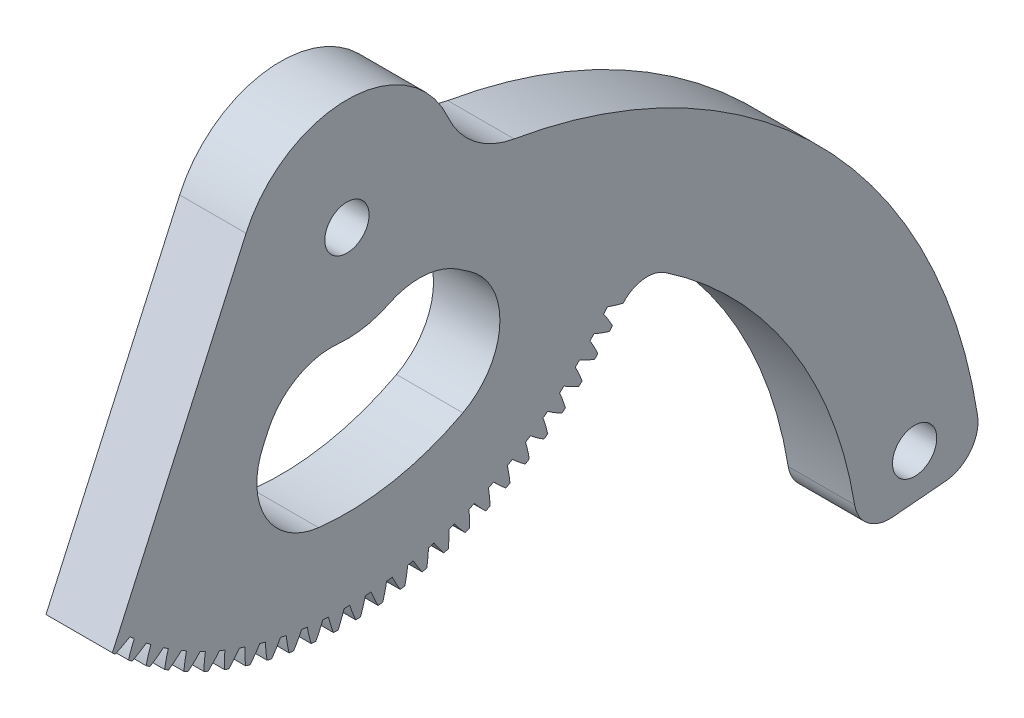
SolidWorks part; units mm, degrees
ref_plane "Plane1" through (0, 0, 0) normal (0, 0, 1) x (1, 0, 0)
ref_plane "Plane2" through (0, 0, 0) normal (0, 1, 0) x (1, 0, 0)
ref_plane "Plane3" through (0, 0, 0) normal (1, 0, 0) x (0, 0, -1)
sketch "HoldingSke" plane through (0, 0, 0) normal (0, 1, 0) x (1, 0, 0)
  line L0 (0, 0) -> (-0.1045, -0.9945)
  line L1 (-15, 0) -> (100, 0) construction
  line L2 (0, 0) -> (-2.1039, 2.3779)
  line L3 (0, 0) -> (-11.863, 4.5341)
  line L4 (0, 0) -> (-0.9027, 8.5887)
  line L5 (0, 0) -> (-46.8476, -17.4728)
  line L6 (0, 0) -> (-10.5278, -7.1032)
  line L7 (-2.1039, 2.3779) -> (8.6586, 51.2059)
  line L8 (-76.2, 54.61) -> (-76.1, 54.61)
  line L9 (-71.009, 38.7566) -> (-53.1078, 45.2721)
  line L10 (-76.2, 71.12) -> (104.1128, 71.12)
  line L11 (0, 0) -> (-12.7, 0)
  line L12 (-76.2, 101.6) -> (-76.162, 101.6)
  line L13 (24.9733, 27.94) -> (52.9518, 28.4284)
  line L14 (24.9733, 27.94) -> (24.9743, 27.94)
  line L15 (24.9733, 27.94) -> (100.4006, 29.5858)
  line L16 (-63.627, -1) -> (-12.827, -1)
  circle A0 centre (0, 0) radius 0.4
  circle A1 centre (0, 0) radius 37.5
  circle A2 centre (0, 0) radius 37.5
  circle A3 centre (0, 0) radius 0.4
  dimension "MHD" = 75
  dimension "Hub_dia" = 75
  dimension "Bore" = 0.8
  dimension "MBD" = 0.8
  dimension "Num_teeth" = 96
  dimension "Pitch" = 1
  dimension "Overall_len" = 50
  dimension "Show_teeth" = 96
  dimension "Thickness" = 12.7
  dimension "OAL" = 50.0001
  dimension "T_dim" = 0.1
  dimension "Ap" = 20
  dimension "H" = 19.05
  dimension "Pitch_radius" = 180.3128
  dimension "Width" = 12.7
  dimension "Backlash" = 0.038
  dimension "Addendum_fac" = 1
  dimension "Dedendum_fac" = 1.25
  dimension "Clearance_fac" = 0.25
  dimension "Dedendum_add" = 0.001
  dimension "Module" = 1
sketch "BasProSke" plane through (0, 0, 0) normal (0, 1, 0) x (1, 0, 0)
  line L0 (-10, 0) -> (60, 0) construction
  line L1 (0, 0) -> (0, 49)
  line L2 (0, 0) -> (12.7, 0)
  line L3 (12.7, 0) -> (12.7, 49)
  line L4 (12.7, 49) -> (0, 49)
  dimension "Thickness" = 12.7
  dimension "Diameter" = 98
revolve "Base-Revolve" add sketch "BasProSke" angle 360 about L0
sketch "TooCutSke" plane through (0, 0, 0) normal (1, 0, 0) x (0, 0, -1)
  line L1 (0, 0) -> (0, 107) construction
  line L2 (0, 0) -> (-0.8519, 47.9924) construction
  line L3 (0, 0) -> (-3.1407, 95.9378) construction
  line L4 (-0.8519, 47.9924) -> (-1.5703, 47.9689) construction
  arc A0 (0.4157, 46.7472) -> (-0.4157, 46.7472) centre (0, 0) ccw
  arc A1 (1.2815, 49.0086) -> (-1.2815, 49.0086) centre (0, 0) ccw
  circle A2 centre (0, 0) radius 48 construction
  circle A3 centre (0, 0) radius 45.1052 construction
  arc A4 (-0.4157, 46.7472) -> (-1.2815, 49.0086) centre (-18.7436, 41.0264) ccw
  arc A5 (1.2815, 49.0086) -> (0.4157, 46.7472) centre (18.7436, 41.0264) ccw
  dimension "Root_dia" = 93.498
  dimension "Overcut_dia" = 98.0508
  dimension "Pitch_dia" = 96
  dimension "Base_dia" = 90.2105
  dimension "Flank_rad" = 19.2
  dimension "Half_ang" = 1.875
  dimension "Half_CT" = 0.7189
extrude "ToothCut" cut sketch "TooCutSke" along normal through all
fillet "Breaks" [suppressed] radius 0.02
fillet "RootFillets" [suppressed] radius 0.251
pattern_circular "TeethCuts" count 96 every 3.75 about axis through (-10, 0, 0) along (1, 0, 0) of "ToothCut", "RootFillets", "Breaks"
sketch "HubNeaOneSke" plane through (0, 0, 0) normal (-1, 0, 0) x (0, 0, 1)
  circle A0 centre (0, 0) radius 37.5
  dimension "Diameter" = 75
extrude "HubNearOne" [suppressed] add sketch "HubNeaOneSke" along normal blind 37.3001
sketch "HubNeaBotSke" plane through (0, 0, 0) normal (-1, 0, 0) x (0, 0, 1)
  circle A0 centre (0, 0) radius 37.5
  dimension "Diameter" = 75
extrude "HubNearBoth" [suppressed] add sketch "HubNeaBotSke" along normal blind 18.65
ref_plane "FarPln" through (12.7, 0, 0) normal (1, 0, 0) x (0, 0, -1)
sketch "HubFarSke" plane through (12.7, 0, 0) normal (1, 0, 0) x (0, 0, -1)
  circle A0 centre (0, 0) radius 37.5
  dimension "Diameter" = 75
extrude "HubFar" [suppressed] add sketch "HubFarSke" along normal blind 18.65
sketch "BorSke" plane through (0, 0, 0) normal (1, 0, 0) x (0, 0, -1)
  circle A0 centre (0, 0) radius 0.4
  dimension "Diameter" = 0.8
extrude "Bore" cut sketch "BorSke" along normal mid plane 100.0001
sketch "KeySke" plane through (0, 0, 0) normal (1, 0, 0) x (0, 0, -1)
  line L0 (-0.05, 0) -> (-0.05, 0.5)
  line L1 (-0.05, 0.5) -> (0.05, 0.5)
  line L2 (0.05, 0.5) -> (0.05, 0)
  line L3 (0, 0) -> (0, 34) construction
  line L4 (-0.05, 0) -> (0.05, 0)
  dimension "Offset" = 0.5
  dimension "Width" = 0.1
extrude "Keyway" [suppressed] cut sketch "KeySke" along normal mid plane 100.0001
pattern_circular "Keyway2" [suppressed] count 2 every 90 about axis through (-10, 0, 0) along (1, 0, 0)
sketch "Croquis2" plane through (12.7, 0, 0) normal (1, 0, 0) x (0, 0, -1)
  line L4 (78.2913, -74.7181) -> (85.9012, -74.0523)
  line L5 (-14.4729, 6.923) -> (-33.6475, -35.6208)
  arc A0 (-33.6475, -35.6208) -> (40.4538, -27.7628) centre (0, 0.4) ccw
  arc A1 (48.3959, -8.954) -> (40.4538, -27.7628) centre (0, 0.4) ccw
  arc A2 (-33.7385, -35.5347) -> (-33.252, -35.9904) centre (0, 0) ccw construction
  arc A66 (85.9012, -74.0523) -> (90.4783, -68.2125) centre (85.4584, -68.9917) ccw
  arc A67 (90.4783, -68.2125) -> (23.9847, -0.5832) centre (10.16, -80.6788) ccw
  arc A68 (14.5249, 6.8066) -> (23.9847, -0.5832) centre (26.1448, 11.9318) ccw
  arc A69 (14.5249, 6.8066) -> (-14.4729, 6.923) centre (0, 0.4) ccw
  arc A96 (45.6754, -28.0395) -> (40.4538, -27.7628) centre (42.8342, -32.2506) ccw
  arc A97 (72.8346, -70.4738) -> (45.6754, -28.0395) centre (10.16, -80.6788) ccw
  arc A98 (72.8346, -70.4738) -> (78.2913, -74.7181) centre (77.8486, -69.6574) ccw
extrude "Cortar-Extruir1" cut sketch "Croquis2" against normal through all contours A69 A68 A67 A1 L5
sketch "Croquis3" plane through (12.7, 0, 0) normal (1, 0, 0) x (0, 0, -1)
  line L0 (78.2913, -74.7181) -> (85.9012, -74.0523) construction
  line L1 (78.2913, -74.7181) -> (85.9012, -74.0523)
  line L2 (23.9847, -0.5832) -> (26.1016, -24.7798)
  line L4 (39.6344, -28.8117) -> (26.1016, -24.7798)
  arc A1 (90.4783, -68.2125) -> (23.9847, -0.5832) centre (10.16, -80.6788) ccw construction
  arc A2 (85.9012, -74.0523) -> (90.4783, -68.2125) centre (85.4584, -68.9917) ccw construction
  arc A3 (72.8346, -70.4738) -> (78.2913, -74.7181) centre (77.8486, -69.6574) ccw construction
  arc A4 (72.8346, -70.4738) -> (45.6754, -28.0395) centre (10.16, -80.6788) ccw construction
  arc A6 (90.4783, -68.2125) -> (23.9847, -0.5832) centre (10.16, -80.6788) ccw
  arc A7 (85.9012, -74.0523) -> (90.4783, -68.2125) centre (85.4584, -68.9917) ccw
  arc A8 (72.8346, -70.4738) -> (78.2913, -74.7181) centre (77.8486, -69.6574) ccw
  arc A9 (72.8346, -70.4738) -> (45.6754, -28.0395) centre (10.16, -80.6788) ccw
  arc A13 (39.6344, -28.8117) -> (45.6754, -28.0395) centre (43.0946, -31.8647) cw
extrude "Saliente-Extruir1" add sketch "Croquis3" against normal through all
sketch "Croquis4" plane through (12.7, 0, 0) normal (1, 0, 0) x (0, 0, -1)
  line L0 (78.2913, -74.7181) -> (85.9012, -74.0523) construction
  circle A0 centre (0, 0.4) radius 3.175
  circle A1 centre (81.4431, -68.0681) radius 3.175
  arc A2 (90.4783, -68.2125) -> (23.9847, -0.5832) centre (10.16, -80.6788) ccw construction
  arc A3 (90.4783, -68.2125) -> (23.9847, -0.5832) centre (10.16, -80.6788) ccw construction
  circle A4 centre (10.16, -80.6788) radius 72.39 construction
  circle A5 centre (10.16, -80.6788) radius 81.715 construction
  arc A6 (14.5249, 6.8066) -> (-14.4729, 6.923) centre (0, 0.4) ccw construction
  dimension "D1" = 6.35
  dimension "D2" = 6.35
  dimension "D3" = 144.78
  dimension "D4" = 163.43
extrude "Cortar-Extruir2" cut sketch "Croquis4" against normal through all
sketch "Croquis5" plane through (0, 0, 0) normal (1, 0, 0) x (0, 0, -1)
  circle A1 centre (81.4431, -68.0681) radius 5
  dimension "D1" = 10
extrude "Cortar-Extruir3" cut sketch "Croquis5" along normal blind 6
ref_plane "Plano1" through (6.35, 0, 0) normal (1, 0, 0) x (0, 0, -1)
sketch "Croquis6" plane through (6.35, 0, 0) normal (1, 0, 0) x (0, 0, -1)
  circle A0 centre (0, 0.4) radius 49.2915 construction
  circle A1 centre (0, 0.4) radius 48.2915
  dimension "D1" = 1
sketch "Croquis7" plane through (12.7, 0, 0) normal (1, 0, 0) x (0, 0, -1)
  line L0 (-12.0435, -20.8056) -> (-11.3475, -19.2613)
  line L1 (17.5581, -13.8325) -> (16.0371, -12.8013)
  arc A0 (-1.2964, -13.414) -> (6.0586, -12.082) centre (0, 0.4) ccw
  arc A1 (-4.0752, -34.8484) -> (16.6343, -30.9426) centre (0, 0.4) ccw
  arc A2 (17.5581, -13.8325) -> (16.6343, -30.9426) centre (11.9463, -22.1095) cw
  arc A3 (-12.0435, -20.8056) -> (-4.0752, -34.8484) centre (-2.9267, -24.9145) ccw
  arc A4 (-11.3475, -19.2613) -> (-1.2964, -13.414) centre (-2.2307, -23.3703) cw
  arc A5 (16.0371, -12.8013) -> (6.0586, -12.082) centre (10.4253, -21.0782) ccw
  dimension "D1" = 10
extrude "Cortar-Extruir4" cut sketch "Croquis7" against normal up to surface (12.7 mm away)
sketch "Croquis11" plane through (12.7, 0, 0) normal (1, 0, 0) x (0, 0, -1)
  line L2 (78.2913, -74.7181) -> (85.9012, -74.0523)
  line L3 (-14.4729, 6.923) -> (-33.6475, -35.6208)
  line L4 (78.2913, -74.7181) -> (85.9012, -74.0523)
  line L5 (-14.4729, 6.923) -> (-33.6475, -35.6208)
  arc A111 (36.834, -28.7876) -> (37.3401, -28.1281) centre (0, 0) ccw
  arc A112 (37.3401, -28.1281) -> (39.6344, -28.8117) centre (43.9588, -10.105) ccw
  arc A113 (45.6754, -28.0395) -> (39.6344, -28.8117) centre (43.0946, -31.8647) ccw
  arc A114 (72.8346, -70.4738) -> (45.6754, -28.0395) centre (10.16, -80.6788) ccw
  arc A115 (72.8346, -70.4738) -> (78.2913, -74.7181) centre (77.8486, -69.6574) ccw
  arc A116 (85.9012, -74.0523) -> (90.4783, -68.2125) centre (85.4584, -68.9917) ccw
  arc A117 (90.4783, -68.2125) -> (23.9847, -0.5832) centre (10.16, -80.6788) ccw
  arc A118 (14.5249, 6.8066) -> (23.9847, -0.5832) centre (26.1448, 11.9318) ccw
  arc A119 (14.5249, 6.8066) -> (-14.4729, 6.923) centre (0, 0.4) ccw
  arc A120 (-33.6475, -35.6208) -> (-33.252, -35.9904) centre (0, 0) ccw
  arc A121 (-33.252, -35.9904) -> (-31.1351, -34.8723) centre (-41.1427, -18.4867) ccw
  arc A122 (-31.1351, -34.8723) -> (-30.51, -35.4204) centre (0, 0) ccw
  arc A123 (-30.51, -35.4204) -> (-31.3422, -37.6652) centre (-12.9584, -43.2037) ccw
  arc A124 (-31.3422, -37.6652) -> (-30.8269, -38.0881) centre (0, 0) ccw
  arc A125 (-30.8269, -38.0881) -> (-28.7876, -36.834) centre (-39.8455, -21.138) ccw
  arc A126 (-28.7876, -36.834) -> (-28.1281, -37.3401) centre (0, 0) ccw
  arc A127 (-28.1281, -37.3401) -> (-28.8117, -39.6344) centre (-10.105, -43.9588) ccw
  arc A128 (-28.8117, -39.6344) -> (-28.2698, -40.0227) centre (0, 0) ccw
  arc A129 (-28.2698, -40.0227) -> (-26.3169, -38.6379) centre (-38.3777, -23.6988) ccw
  arc A130 (-26.3169, -38.6379) -> (-25.6257, -39.0998) centre (0, 0) ccw
  arc A131 (-25.6257, -39.0998) -> (-26.1578, -41.4339) centre (-7.2083, -44.5255) ccw
  arc A132 (-26.1578, -41.4339) -> (-25.5917, -41.7859) centre (0, 0) ccw
  arc A133 (-25.5917, -41.7859) -> (-23.7336, -40.2764) centre (-36.7456, -26.1581) ccw
  arc A134 (-23.7336, -40.2764) -> (-23.0136, -40.6921) centre (0, 0) ccw
  arc A135 (-23.0136, -40.6921) -> (-23.3918, -43.056) centre (-4.2808, -44.9017) ccw
  arc A136 (-23.3918, -43.056) -> (-22.804, -43.3703) centre (0, 0) ccw
  arc A137 (-22.804, -43.3703) -> (-21.0485, -41.7424) centre (-34.9561, -28.5053) ccw
  arc A138 (-21.0485, -41.7424) -> (-20.3029, -42.1101) centre (0, 0) ccw
  arc A139 (-20.3029, -42.1101) -> (-20.5258, -44.4937) centre (-1.3349, -45.0855) ccw
  arc A140 (-20.5258, -44.4937) -> (-19.9186, -44.7688) centre (0, 0) ccw
  arc A141 (-19.9186, -44.7688) -> (-18.2734, -43.0297) centre (-33.0169, -30.7305) ccw
  arc A142 (-18.2734, -43.0297) -> (-17.5053, -43.3478) centre (0, 0) ccw
  arc A143 (-17.5053, -43.3478) -> (-17.5718, -45.7409) centre (1.6167, -45.0763) ccw
  arc A144 (-17.5718, -45.7409) -> (-16.9479, -45.9757) centre (0, 0) ccw
  arc A145 (-16.9479, -45.9757) -> (-15.42, -44.1327) centre (-30.9363, -32.8242) ccw
  arc A146 (-15.42, -44.1327) -> (-14.6328, -44.3999) centre (0, 0) ccw
  arc A147 (-14.6328, -44.3999) -> (-14.5426, -46.7922) centre (4.5614, -44.874) ccw
  arc A148 (-14.5426, -46.7922) -> (-13.9047, -46.9857) centre (0, 0) ccw
  arc A149 (-13.9047, -46.9857) -> (-12.5006, -45.0467) centre (-28.7233, -34.7772) ccw
  arc A150 (-12.5006, -45.0467) -> (-11.6976, -45.2619) centre (0, 0) ccw
  arc A151 (-11.6976, -45.2619) -> (-11.4511, -47.6432) centre (7.4865, -44.4796) ccw
  arc A152 (-11.4511, -47.6432) -> (-10.8019, -47.7946) centre (0, 0) ccw
  arc A153 (-10.8019, -47.7946) -> (-9.5276, -45.7678) centre (-26.3873, -36.5813) ccw
  arc A154 (-9.5276, -45.7678) -> (-8.7122, -45.93) centre (0, 0) ccw
  arc A155 (-8.7122, -45.93) -> (-8.3105, -48.2901) centre (10.3796, -43.8947) ccw
  arc A156 (-8.3105, -48.2901) -> (-7.6528, -48.3987) centre (0, 0) ccw
  arc A157 (-7.6528, -48.3987) -> (-6.5138, -46.293) centre (-23.9382, -38.2288) ccw
  arc A158 (-6.5138, -46.293) -> (-5.6896, -46.4015) centre (0, 0) ccw
  arc A159 (-5.6896, -46.4015) -> (-5.1344, -48.7303) centre (13.2282, -43.1219) ccw
  arc A160 (-5.1344, -48.7303) -> (-4.471, -48.7956) centre (0, 0) ccw
  arc A161 (-4.471, -48.7956) -> (-3.4722, -46.6199) centre (-21.3867, -39.7126) ccw
  arc A162 (-3.4722, -46.6199) -> (-2.6426, -46.6742) centre (0, 0) ccw
  arc A163 (-2.6426, -46.6742) -> (-1.9363, -48.9617) centre (16.0202, -42.1644) ccw
  arc A164 (-1.9363, -48.9617) -> (-1.2701, -48.9835) centre (0, 0) ccw
  arc A165 (-1.2701, -48.9835) -> (-0.4157, -46.7472) centre (-18.7436, -41.0264) ccw
  arc A166 (-0.4157, -46.7472) -> (0.4157, -46.7472) centre (0, 0) ccw
  arc A167 (0.4157, -46.7472) -> (1.2701, -48.9835) centre (18.7436, -41.0264) ccw
  arc A168 (1.2701, -48.9835) -> (1.9363, -48.9617) centre (0, 0) ccw
  arc A169 (1.9363, -48.9617) -> (2.6426, -46.6742) centre (-16.0202, -42.1644) ccw
  arc A170 (2.6426, -46.6742) -> (3.4722, -46.6199) centre (0, 0) ccw
  arc A171 (3.4722, -46.6199) -> (4.471, -48.7956) centre (21.3867, -39.7126) ccw
  arc A172 (4.471, -48.7956) -> (5.1344, -48.7303) centre (0, 0) ccw
  arc A173 (5.1344, -48.7303) -> (5.6896, -46.4015) centre (-13.2282, -43.1219) ccw
  arc A174 (5.6896, -46.4015) -> (6.5138, -46.293) centre (0, 0) ccw
  arc A175 (6.5138, -46.293) -> (7.6528, -48.3987) centre (23.9382, -38.2288) ccw
  arc A176 (7.6528, -48.3987) -> (8.3105, -48.2901) centre (0, 0) ccw
  arc A177 (8.3105, -48.2901) -> (8.7122, -45.93) centre (-10.3796, -43.8947) ccw
  arc A178 (8.7122, -45.93) -> (9.5276, -45.7678) centre (0, 0) ccw
  arc A179 (9.5276, -45.7678) -> (10.8019, -47.7946) centre (26.3873, -36.5813) ccw
  arc A180 (10.8019, -47.7946) -> (11.4511, -47.6432) centre (0, 0) ccw
  arc A181 (11.4511, -47.6432) -> (11.6976, -45.2619) centre (-7.4865, -44.4796) ccw
  arc A182 (11.6976, -45.2619) -> (12.5006, -45.0467) centre (0, 0) ccw
  arc A183 (12.5006, -45.0467) -> (13.9047, -46.9857) centre (28.7233, -34.7772) ccw
  arc A184 (13.9047, -46.9857) -> (14.5426, -46.7922) centre (0, 0) ccw
  arc A185 (14.5426, -46.7922) -> (14.6328, -44.3999) centre (-4.5614, -44.874) ccw
  arc A186 (14.6328, -44.3999) -> (15.42, -44.1327) centre (0, 0) ccw
  arc A187 (15.42, -44.1327) -> (16.9479, -45.9757) centre (30.9363, -32.8242) ccw
  arc A188 (16.9479, -45.9757) -> (17.5718, -45.7409) centre (0, 0) ccw
  arc A189 (17.5718, -45.7409) -> (17.5053, -43.3478) centre (-1.6167, -45.0763) ccw
  arc A190 (17.5053, -43.3478) -> (18.2734, -43.0297) centre (0, 0) ccw
  arc A191 (18.2734, -43.0297) -> (19.9186, -44.7688) centre (33.0169, -30.7305) ccw
  arc A192 (19.9186, -44.7688) -> (20.5258, -44.4937) centre (0, 0) ccw
  arc A193 (20.5258, -44.4937) -> (20.3029, -42.1101) centre (1.3349, -45.0855) ccw
  arc A194 (20.3029, -42.1101) -> (21.0485, -41.7424) centre (0, 0) ccw
  arc A195 (21.0485, -41.7424) -> (22.804, -43.3703) centre (34.9561, -28.5053) ccw
  arc A196 (22.804, -43.3703) -> (23.3918, -43.056) centre (0, 0) ccw
  arc A197 (23.3918, -43.056) -> (23.0136, -40.6921) centre (4.2808, -44.9017) ccw
  arc A198 (23.0136, -40.6921) -> (23.7336, -40.2764) centre (0, 0) ccw
  arc A199 (23.7336, -40.2764) -> (25.5917, -41.7859) centre (36.7456, -26.1581) ccw
  arc A200 (25.5917, -41.7859) -> (26.1578, -41.4339) centre (0, 0) ccw
  arc A201 (26.1578, -41.4339) -> (25.6257, -39.0998) centre (7.2083, -44.5255) ccw
  arc A202 (25.6257, -39.0998) -> (26.3169, -38.6379) centre (0, 0) ccw
  arc A203 (26.3169, -38.6379) -> (28.2698, -40.0227) centre (38.3777, -23.6988) ccw
  arc A204 (28.2698, -40.0227) -> (28.8117, -39.6344) centre (0, 0) ccw
  arc A205 (28.8117, -39.6344) -> (28.1281, -37.3401) centre (10.105, -43.9588) ccw
  arc A206 (28.1281, -37.3401) -> (28.7876, -36.834) centre (0, 0) ccw
  arc A207 (28.7876, -36.834) -> (30.8269, -38.0881) centre (39.8455, -21.138) ccw
  arc A208 (30.8269, -38.0881) -> (31.3422, -37.6652) centre (0, 0) ccw
  arc A209 (31.3422, -37.6652) -> (30.51, -35.4204) centre (12.9584, -43.2037) ccw
  arc A210 (30.51, -35.4204) -> (31.1351, -34.8723) centre (0, 0) ccw
  arc A211 (31.1351, -34.8723) -> (33.252, -35.9904) centre (41.1427, -18.4867) ccw
  arc A212 (33.252, -35.9904) -> (33.7385, -35.5347) centre (0, 0) ccw
  arc A213 (33.7385, -35.5347) -> (32.7613, -33.3491) centre (15.7563, -42.2637) ccw
  arc A214 (32.7613, -33.3491) -> (33.3491, -32.7613) centre (0, 0) ccw
  arc A215 (33.3491, -32.7613) -> (35.5347, -33.7385) centre (42.2637, -15.7563) ccw
  arc A216 (35.5347, -33.7385) -> (35.9904, -33.252) centre (0, 0) ccw
  arc A217 (35.9904, -33.252) -> (34.8723, -31.1351) centre (18.4867, -41.1427) ccw
  arc A218 (34.8723, -31.1351) -> (35.4204, -30.51) centre (0, 0) ccw
  arc A219 (35.4204, -30.51) -> (37.6652, -31.3422) centre (43.2037, -12.9584) ccw
  arc A220 (37.6652, -31.3422) -> (38.0881, -30.8269) centre (0, 0) ccw
  arc A221 (38.0881, -30.8269) -> (36.834, -28.7876) centre (21.138, -39.8455) ccw
  arc A222 (36.834, -28.7876) -> (37.3401, -28.1281) centre (0, 0) ccw
  arc A223 (37.3401, -28.1281) -> (39.6344, -28.8117) centre (43.9588, -10.105) ccw
  arc A224 (45.6754, -28.0395) -> (39.6344, -28.8117) centre (43.0946, -31.8647) ccw
  arc A225 (72.8346, -70.4738) -> (45.6754, -28.0395) centre (10.16, -80.6788) ccw
  arc A226 (72.8346, -70.4738) -> (78.2913, -74.7181) centre (77.8486, -69.6574) ccw
  arc A227 (85.9012, -74.0523) -> (90.4783, -68.2125) centre (85.4584, -68.9917) ccw
  arc A228 (90.4783, -68.2125) -> (23.9847, -0.5832) centre (10.16, -80.6788) ccw
  arc A229 (14.5249, 6.8066) -> (23.9847, -0.5832) centre (26.1448, 11.9318) ccw
  arc A230 (14.5249, 6.8066) -> (-14.4729, 6.923) centre (0, 0.4) ccw
  arc A231 (-33.6475, -35.6208) -> (-33.252, -35.9904) centre (0, 0) ccw
  arc A232 (-33.252, -35.9904) -> (-31.1351, -34.8723) centre (-41.1427, -18.4867) ccw
  arc A233 (-31.1351, -34.8723) -> (-30.51, -35.4204) centre (0, 0) ccw
  arc A234 (-30.51, -35.4204) -> (-31.3422, -37.6652) centre (-12.9584, -43.2037) ccw
  arc A235 (-31.3422, -37.6652) -> (-30.8269, -38.0881) centre (0, 0) ccw
  arc A236 (-30.8269, -38.0881) -> (-28.7876, -36.834) centre (-39.8455, -21.138) ccw
  arc A237 (-28.7876, -36.834) -> (-28.1281, -37.3401) centre (0, 0) ccw
  arc A238 (-28.1281, -37.3401) -> (-28.8117, -39.6344) centre (-10.105, -43.9588) ccw
  arc A239 (-28.8117, -39.6344) -> (-28.2698, -40.0227) centre (0, 0) ccw
  arc A240 (-28.2698, -40.0227) -> (-26.3169, -38.6379) centre (-38.3777, -23.6988) ccw
  arc A241 (-26.3169, -38.6379) -> (-25.6257, -39.0998) centre (0, 0) ccw
  arc A242 (-25.6257, -39.0998) -> (-26.1578, -41.4339) centre (-7.2083, -44.5255) ccw
  arc A243 (-26.1578, -41.4339) -> (-25.5917, -41.7859) centre (0, 0) ccw
  arc A244 (-25.5917, -41.7859) -> (-23.7336, -40.2764) centre (-36.7456, -26.1581) ccw
  arc A245 (-23.7336, -40.2764) -> (-23.0136, -40.6921) centre (0, 0) ccw
  arc A246 (-23.0136, -40.6921) -> (-23.3918, -43.056) centre (-4.2808, -44.9017) ccw
  arc A247 (-23.3918, -43.056) -> (-22.804, -43.3703) centre (0, 0) ccw
  arc A248 (-22.804, -43.3703) -> (-21.0485, -41.7424) centre (-34.9561, -28.5053) ccw
  arc A249 (-21.0485, -41.7424) -> (-20.3029, -42.1101) centre (0, 0) ccw
  arc A250 (-20.3029, -42.1101) -> (-20.5258, -44.4937) centre (-1.3349, -45.0855) ccw
  arc A251 (-20.5258, -44.4937) -> (-19.9186, -44.7688) centre (0, 0) ccw
  arc A252 (-19.9186, -44.7688) -> (-18.2734, -43.0297) centre (-33.0169, -30.7305) ccw
  arc A253 (-18.2734, -43.0297) -> (-17.5053, -43.3478) centre (0, 0) ccw
  arc A254 (-17.5053, -43.3478) -> (-17.5718, -45.7409) centre (1.6167, -45.0763) ccw
  arc A255 (-17.5718, -45.7409) -> (-16.9479, -45.9757) centre (0, 0) ccw
  arc A256 (-16.9479, -45.9757) -> (-15.42, -44.1327) centre (-30.9363, -32.8242) ccw
  arc A257 (-15.42, -44.1327) -> (-14.6328, -44.3999) centre (0, 0) ccw
  arc A258 (-14.6328, -44.3999) -> (-14.5426, -46.7922) centre (4.5614, -44.874) ccw
  arc A259 (-14.5426, -46.7922) -> (-13.9047, -46.9857) centre (0, 0) ccw
  arc A260 (-13.9047, -46.9857) -> (-12.5006, -45.0467) centre (-28.7233, -34.7772) ccw
  arc A261 (-12.5006, -45.0467) -> (-11.6976, -45.2619) centre (0, 0) ccw
  arc A262 (-11.6976, -45.2619) -> (-11.4511, -47.6432) centre (7.4865, -44.4796) ccw
  arc A263 (-11.4511, -47.6432) -> (-10.8019, -47.7946) centre (0, 0) ccw
  arc A264 (-10.8019, -47.7946) -> (-9.5276, -45.7678) centre (-26.3873, -36.5813) ccw
  arc A265 (-9.5276, -45.7678) -> (-8.7122, -45.93) centre (0, 0) ccw
  arc A266 (-8.7122, -45.93) -> (-8.3105, -48.2901) centre (10.3796, -43.8947) ccw
  arc A267 (-8.3105, -48.2901) -> (-7.6528, -48.3987) centre (0, 0) ccw
  arc A268 (-7.6528, -48.3987) -> (-6.5138, -46.293) centre (-23.9382, -38.2288) ccw
  arc A269 (-6.5138, -46.293) -> (-5.6896, -46.4015) centre (0, 0) ccw
  arc A270 (-5.6896, -46.4015) -> (-5.1344, -48.7303) centre (13.2282, -43.1219) ccw
  arc A271 (-5.1344, -48.7303) -> (-4.471, -48.7956) centre (0, 0) ccw
  arc A272 (-4.471, -48.7956) -> (-3.4722, -46.6199) centre (-21.3867, -39.7126) ccw
  arc A273 (-3.4722, -46.6199) -> (-2.6426, -46.6742) centre (0, 0) ccw
  arc A274 (-2.6426, -46.6742) -> (-1.9363, -48.9617) centre (16.0202, -42.1644) ccw
  arc A275 (-1.9363, -48.9617) -> (-1.2701, -48.9835) centre (0, 0) ccw
  arc A276 (-1.2701, -48.9835) -> (-0.4157, -46.7472) centre (-18.7436, -41.0264) ccw
  arc A277 (-0.4157, -46.7472) -> (0.4157, -46.7472) centre (0, 0) ccw
  arc A278 (0.4157, -46.7472) -> (1.2701, -48.9835) centre (18.7436, -41.0264) ccw
  arc A279 (1.2701, -48.9835) -> (1.9363, -48.9617) centre (0, 0) ccw
  arc A280 (1.9363, -48.9617) -> (2.6426, -46.6742) centre (-16.0202, -42.1644) ccw
  arc A281 (2.6426, -46.6742) -> (3.4722, -46.6199) centre (0, 0) ccw
  arc A282 (3.4722, -46.6199) -> (4.471, -48.7956) centre (21.3867, -39.7126) ccw
  arc A283 (4.471, -48.7956) -> (5.1344, -48.7303) centre (0, 0) ccw
  arc A284 (5.1344, -48.7303) -> (5.6896, -46.4015) centre (-13.2282, -43.1219) ccw
  arc A285 (5.6896, -46.4015) -> (6.5138, -46.293) centre (0, 0) ccw
  arc A286 (6.5138, -46.293) -> (7.6528, -48.3987) centre (23.9382, -38.2288) ccw
  arc A287 (7.6528, -48.3987) -> (8.3105, -48.2901) centre (0, 0) ccw
  arc A288 (8.3105, -48.2901) -> (8.7122, -45.93) centre (-10.3796, -43.8947) ccw
  arc A289 (8.7122, -45.93) -> (9.5276, -45.7678) centre (0, 0) ccw
  arc A290 (9.5276, -45.7678) -> (10.8019, -47.7946) centre (26.3873, -36.5813) ccw
  arc A291 (10.8019, -47.7946) -> (11.4511, -47.6432) centre (0, 0) ccw
  arc A292 (11.4511, -47.6432) -> (11.6976, -45.2619) centre (-7.4865, -44.4796) ccw
  arc A293 (11.6976, -45.2619) -> (12.5006, -45.0467) centre (0, 0) ccw
  arc A294 (12.5006, -45.0467) -> (13.9047, -46.9857) centre (28.7233, -34.7772) ccw
  arc A295 (13.9047, -46.9857) -> (14.5426, -46.7922) centre (0, 0) ccw
  arc A296 (14.5426, -46.7922) -> (14.6328, -44.3999) centre (-4.5614, -44.874) ccw
  arc A297 (14.6328, -44.3999) -> (15.42, -44.1327) centre (0, 0) ccw
  arc A298 (15.42, -44.1327) -> (16.9479, -45.9757) centre (30.9363, -32.8242) ccw
  arc A299 (16.9479, -45.9757) -> (17.5718, -45.7409) centre (0, 0) ccw
  arc A300 (17.5718, -45.7409) -> (17.5053, -43.3478) centre (-1.6167, -45.0763) ccw
  arc A301 (17.5053, -43.3478) -> (18.2734, -43.0297) centre (0, 0) ccw
  arc A302 (18.2734, -43.0297) -> (19.9186, -44.7688) centre (33.0169, -30.7305) ccw
  arc A303 (19.9186, -44.7688) -> (20.5258, -44.4937) centre (0, 0) ccw
  arc A304 (20.5258, -44.4937) -> (20.3029, -42.1101) centre (1.3349, -45.0855) ccw
  arc A305 (20.3029, -42.1101) -> (21.0485, -41.7424) centre (0, 0) ccw
  arc A306 (21.0485, -41.7424) -> (22.804, -43.3703) centre (34.9561, -28.5053) ccw
  arc A307 (22.804, -43.3703) -> (23.3918, -43.056) centre (0, 0) ccw
  arc A308 (23.3918, -43.056) -> (23.0136, -40.6921) centre (4.2808, -44.9017) ccw
  arc A309 (23.0136, -40.6921) -> (23.7336, -40.2764) centre (0, 0) ccw
  arc A310 (23.7336, -40.2764) -> (25.5917, -41.7859) centre (36.7456, -26.1581) ccw
  arc A311 (25.5917, -41.7859) -> (26.1578, -41.4339) centre (0, 0) ccw
  arc A312 (26.1578, -41.4339) -> (25.6257, -39.0998) centre (7.2083, -44.5255) ccw
  arc A313 (25.6257, -39.0998) -> (26.3169, -38.6379) centre (0, 0) ccw
  arc A314 (26.3169, -38.6379) -> (28.2698, -40.0227) centre (38.3777, -23.6988) ccw
  arc A315 (28.2698, -40.0227) -> (28.8117, -39.6344) centre (0, 0) ccw
  arc A316 (28.8117, -39.6344) -> (28.1281, -37.3401) centre (10.105, -43.9588) ccw
  arc A317 (28.1281, -37.3401) -> (28.7876, -36.834) centre (0, 0) ccw
  arc A318 (28.7876, -36.834) -> (30.8269, -38.0881) centre (39.8455, -21.138) ccw
  arc A319 (30.8269, -38.0881) -> (31.3422, -37.6652) centre (0, 0) ccw
  arc A320 (31.3422, -37.6652) -> (30.51, -35.4204) centre (12.9584, -43.2037) ccw
  arc A321 (30.51, -35.4204) -> (31.1351, -34.8723) centre (0, 0) ccw
  arc A322 (31.1351, -34.8723) -> (33.252, -35.9904) centre (41.1427, -18.4867) ccw
  arc A323 (33.252, -35.9904) -> (33.7385, -35.5347) centre (0, 0) ccw
  arc A324 (33.7385, -35.5347) -> (32.7613, -33.3491) centre (15.7563, -42.2637) ccw
  arc A325 (32.7613, -33.3491) -> (33.3491, -32.7613) centre (0, 0) ccw
  arc A326 (33.3491, -32.7613) -> (35.5347, -33.7385) centre (42.2637, -15.7563) ccw
  arc A327 (35.5347, -33.7385) -> (35.9904, -33.252) centre (0, 0) ccw
  arc A328 (35.9904, -33.252) -> (34.8723, -31.1351) centre (18.4867, -41.1427) ccw
  arc A329 (34.8723, -31.1351) -> (35.4204, -30.51) centre (0, 0) ccw
  arc A330 (35.4204, -30.51) -> (37.6652, -31.3422) centre (43.2037, -12.9584) ccw
  arc A331 (37.6652, -31.3422) -> (38.0881, -30.8269) centre (0, 0) ccw
  arc A332 (38.0881, -30.8269) -> (36.834, -28.7876) centre (21.138, -39.8455) ccw
  dimension "D1" = 0
extrude "Cortar-Extruir5" cut sketch "Croquis11" against normal blind 1.5875
mirror "Simetría1" about plane through (6.35, 0, 0) normal (1, 0, 0) of "Cortar-Extruir5"
equation "' \"Module@HoldingSke\" = 6.35"
equation "' \"Num_teeth@HoldingSke\" = 12"
equation "' \"Ap@HoldingSke\" =  20"
equation "' \"Ap@HoldingSke\" = 20"
equation "' \"Width@HoldingSke\" = 0.5 * 25.4"
equation "' \"Hub_dia@HoldingSke\"= 1 * 25.4"
equation "' \"Hub_dia@HoldingSke\" = 1 * 25.4"
equation "' \"Overall_len@HoldingSke\" = 1.0 * 25.4"
equation "' \"Bore@HoldingSke\" = 0.75 * 25.4"
equation "' \"T_dim@HoldingSke\" = 0.1 * 25.4"
equation "' \"Width@KeySke\" = 0.25 * 25.4"
equation "' \"Show_teeth@HoldingSke\" = 13"
equation "' \"Backlash@HoldingSke\" = 0.009 * 25.4"
equation "' \"Addendum_fac@HoldingSke\" = 1.0"
equation "' \"Dedendum_fac@HoldingSke\" = 1.25"
equation "' \"Dedendum_add@HoldingSke\" = 0.00005 * 25.4"
equation "' \"Clearance_fac@HoldingSke\" = 0.25"
equation "\"Pitch@HoldingSke\" = 1 / \"Module@HoldingSke\""
equation "\"Overcut_dia@TooCutSke\" = (\"Num_teeth@HoldingSke\" + 2 * \"Addendum_fac@HoldingSke\") / \"Pitch@HoldingSke\" + 0.002 * 25.4"
equation "\"Pitch_dia@TooCutSke\" = \"Num_teeth@HoldingSke\" / \"Pitch@HoldingSke\""
equation "\"Base_dia@TooCutSke\" = \"Num_teeth@HoldingSke\" / \"Pitch@HoldingSke\" * cos((\"Ap@HoldingSke\"  * 3.14159265 / 180))"
equation "\"Root_dia@TooCutSke\" = (\"Num_teeth@HoldingSke\" + 2) / \"Pitch@HoldingSke\" - 2 * (\"Addendum_fac@HoldingSke\" + \"Dedendum_fac@HoldingSke\") / \"Pitch@HoldingSke\" - \"Dedendum_add@HoldingSke\" * 2"
equation "\"Half_ang@TooCutSke\" = 180 / \"Num_teeth@HoldingSke\""
equation "\"Half_CT@TooCutSke\" = \"Num_teeth@HoldingSke\" / \"Pitch@HoldingSke\" * sin((3.14159265 / 2 / \"Num_teeth@HoldingSke\")) / 2 - 7 * \"Backlash@HoldingSke\" / 4"
equation "\"Flank_rad@TooCutSke\" = \"Num_teeth@HoldingSke\" / \"Pitch@HoldingSke\" / 5"
equation "\"Radius@RootFillets\" = \"Clearance_fac@HoldingSke\" / \"Pitch@HoldingSke\" + \"Dedendum_add@HoldingSke\""
equation "\"Break_rad@Breaks\" = 0.02 / \"Pitch@HoldingSke\""
equation "\"Thickness@HoldingSke\" = \"Width@HoldingSke\""
equation "\"OAL@HoldingSke\" = \"Thickness@HoldingSke\""
equation "\"MHD@HoldingSke\" = (\"Num_teeth@HoldingSke\" + 2) / \"Pitch@HoldingSke\" - 2 * (\"Addendum_fac@HoldingSke\" + \"Dedendum_fac@HoldingSke\")  / \"Pitch@HoldingSke\" - \"Dedendum_add@HoldingSke\" * 2"
equation "\"MBD@HoldingSke\" = (\"Num_teeth@HoldingSke\" + 2) / \"Pitch@HoldingSke\" - 2 * (\"Addendum_fac@HoldingSke\" + \"Dedendum_fac@HoldingSke\")  / \"Pitch@HoldingSke\" - \"Dedendum_add@HoldingSke\" * 2 - 0.002 * 25.4"
equation "\"MHD@HoldingSke\" = ((sgn( \"MHD@HoldingSke\" - \"Hub_dia@HoldingSke\" )-1)*( \"MHD@HoldingSke\" - \"Hub_dia@HoldingSke\" ))/-2+ \"Hub_dia@HoldingSke\""
equation "\"MBD@HoldingSke\" = ((sgn( \"MBD@HoldingSke\" - \"Bore@HoldingSke\" )-1)*( \"MBD@HoldingSke\" - \"Bore@HoldingSke\" ))/-2+ \"Bore@HoldingSke\""
equation "\"OAL@HoldingSke\" = ((sgn( \"OAL@HoldingSke\" - \"Overall_len@HoldingSke\" )+1)*( \"OAL@HoldingSke\" - \"Overall_len@HoldingSke\" ))/2 + \"Overall_len@HoldingSke\" + 0.000002 * 25.4"
equation "\"Num_teeth@TeethCuts\" = int( \"Show_teeth@HoldingSke\" ) + 1"
equation "\"Num_teeth@TeethCuts\" = ((sgn( \"Num_teeth@TeethCuts\" - \"Num_teeth@HoldingSke\" )-1)*( \"Num_teeth@TeethCuts\" - \"Num_teeth@HoldingSke\" ))/-2+ \"Num_teeth@HoldingSke\""
equation "\"Num_teeth@TeethCuts\" = ((sgn( \"Num_teeth@TeethCuts\" - 2.0)+1)*( \"Num_teeth@TeethCuts\" - 2.0))/2 +2.0"
equation "\"Angle@TeethCuts\" = 360.0 / \"Num_teeth@HoldingSke\""
equation "\"Diameter@BasProSke\" = (\"Num_teeth@HoldingSke\" + 2 * \"Addendum_fac@HoldingSke\") / \"Pitch@HoldingSke\""
equation "\"Thickness@BasProSke\"  = \"Thickness@HoldingSke\""
equation "' \"Fillet_rad@BasProSke\" =  \"Thickness@HoldingSke\" * 0.05"
equation "' \"Fillet_rad@BasProSke\" = \"Thickness@HoldingSke\" * 0.05"
equation "\"MHD@HoldingSke\" = ((sgn( \"MHD@HoldingSke\" - \"Root_dia@TooCutSke\" )-1)*( \"MHD@HoldingSke\" - \"Root_dia@TooCutSke\" ))/-2+ \"Root_dia@TooCutSke\""
equation "\"Diameter@HubNeaOneSke\" = \"MHD@HoldingSke\""
equation "\"Length@HubNearOne\" = \"OAL@HoldingSke\" - \"Thickness@BasProSke\""
equation "\"Diameter@HubNeaBotSke\" = \"MHD@HoldingSke\""
equation "\"Length@HubNearBoth\" = ( \"OAL@HoldingSke\" - \"Thickness@BasProSke\" ) / 2.0"
equation "\"Thickness@FarPln\" = \"Thickness@BasProSke\""
equation "\"Diameter@HubFarSke\" = \"MHD@HoldingSke\""
equation "\"Length@HubFar\" = ( \"OAL@HoldingSke\" - \"Thickness@BasProSke\" ) / 2.0"
equation "\"Diameter@BorSke\" = \"MBD@HoldingSke\""
equation "\"D1@Bore\" = \"OAL@HoldingSke\" * 2.0"
equation "\"D1@Keyway\" = \"OAL@HoldingSke\" * 2.0"
equation "\"Offset@KeySke\" = \"T_dim@HoldingSke\" + \"MBD@HoldingSke\" / 2.0"
